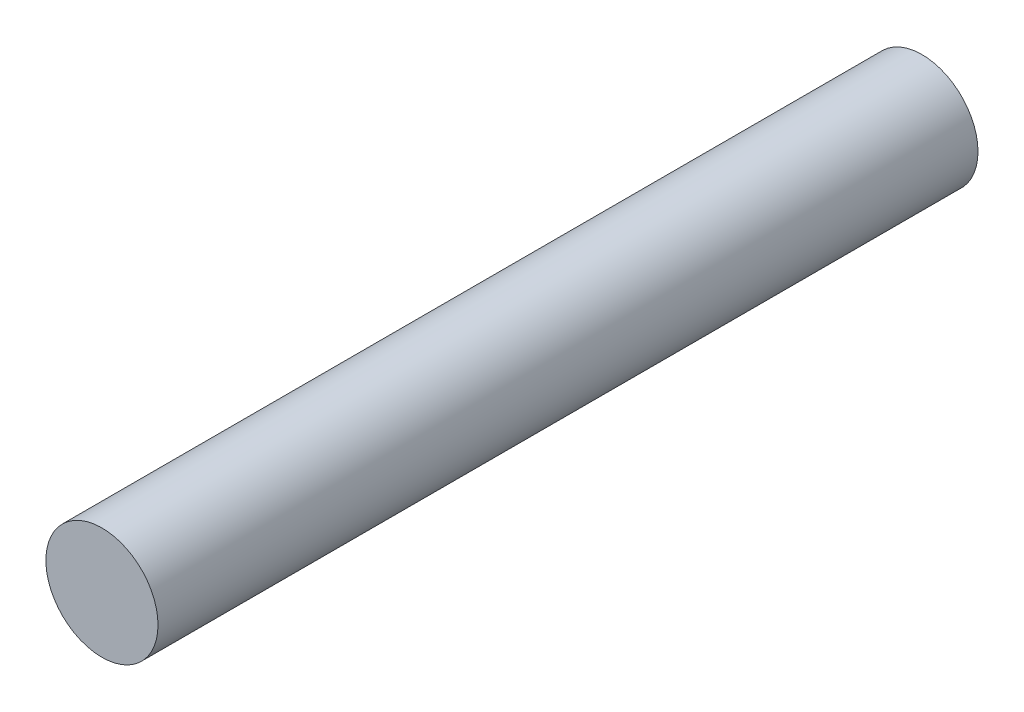
SolidWorks part; units mm, degrees
material "2014 Alloy"
ref_plane "Front Plane" through (0, 0, 0) normal (0, 0, 1) x (1, 0, 0)
ref_plane "Top Plane" through (0, 0, 0) normal (0, 1, 0) x (1, 0, 0)
ref_plane "Right Plane" through (0, 0, 0) normal (1, 0, 0) x (0, 0, -1)
sketch "Sketch1" plane through (0, 0, 0) normal (0, 0, 1) x (1, 0, 0)
  circle A0 centre (0, 0) radius 2.3876
  dimension "D1" = 4.7752
extrude "Extrude1" add sketch "Sketch1" along normal mid plane 34.925
